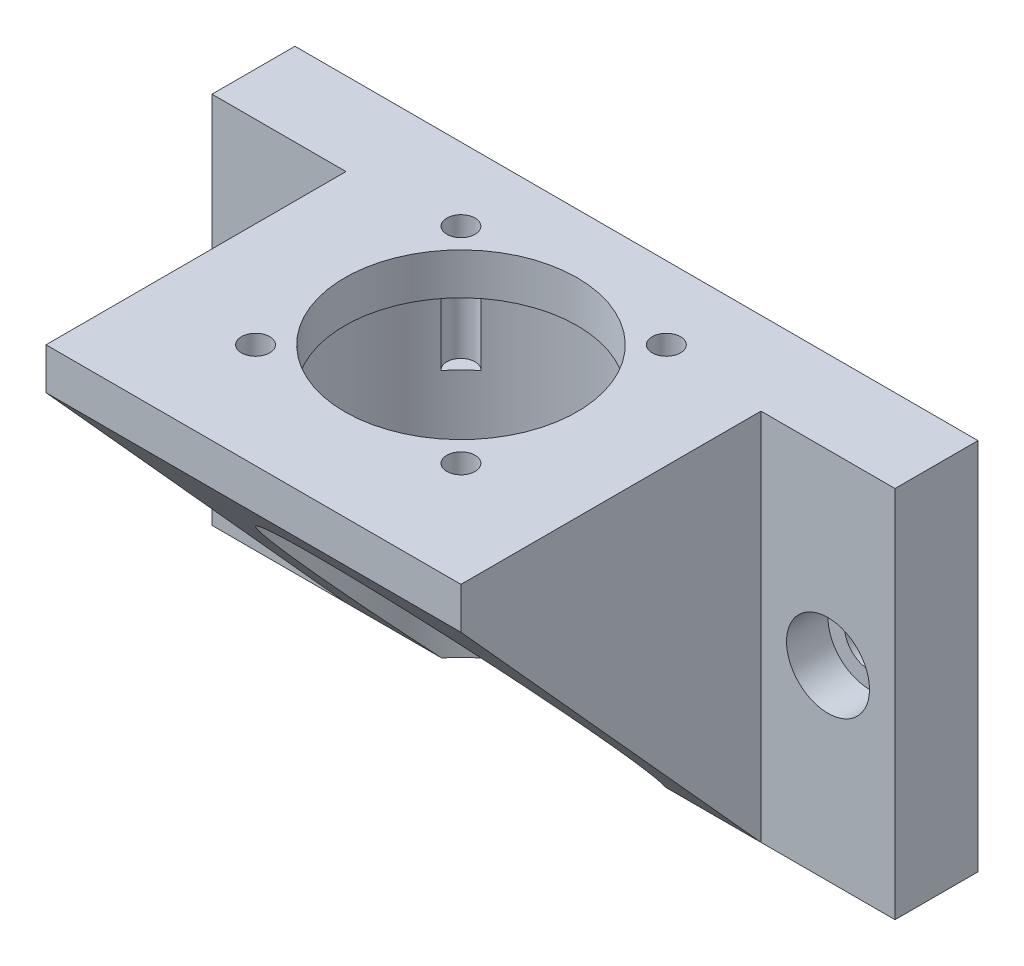
SolidWorks part; units mm, degrees
ref_plane "Спереди" through (0, 0, 0) normal (0, 0, 1) x (1, 0, 0)
ref_plane "Сверху" through (0, 0, 0) normal (0, 1, 0) x (1, 0, 0)
ref_plane "Справа" through (0, 0, 0) normal (1, 0, 0) x (0, 0, -1)
sketch "Эскиз1" plane through (0, 0, 0) normal (0, 1, 0) x (1, 0, 0)
  line L3 (-21.15, 21.15) -> (21.15, 21.15)
  line L6 (-25, 11.15) -> (-25, -25)
  line L7 (21.15, 21.15) -> (41.15, 21.15)
  line L8 (41.15, 21.15) -> (41.15, 11.15)
  line L9 (41.15, 11.15) -> (25, 11.15)
  line L10 (-21.15, 21.15) -> (-41.15, 21.15)
  line L11 (-41.15, 21.15) -> (-41.15, 11.15)
  line L12 (-41.15, 11.15) -> (-25, 11.15)
  line L13 (-25, -25) -> (25, -25)
  line L14 (25, 11.15) -> (25, -25)
  point P0 (0, 0)
  point P5 (0, 0)
  dimension "D3" = 20
  dimension "D4" = 10
  dimension "D5" = 20
  dimension "D6" = 10
extrude "Бобышка-Вытянуть1" add sketch "Эскиз1" along normal blind 45
sketch "Эскиз2" plane through (0, 0, 0) normal (0, -1, 0) x (1, 0, 0)
  circle A0 centre (0, 0) radius 17.5
  dimension "D1" = 35
extrude "Вырез-Вытянуть1" cut sketch "Эскиз2" against normal blind 40
sketch "Эскиз3" plane through (0, 40, 0) normal (0, -1, 0) x (1, 0, 0)
  circle A0 centre (0, 0) radius 14
  dimension "D1" = 28
extrude "Вырез-Вытянуть2" cut sketch "Эскиз3" against normal through all
sketch "Эскиз4" plane through (0, 40, 0) normal (0, -1, 0) x (1, 0, 0)
  line L1 (-17.5, 17.5) -> (17.5, 17.5) construction
  line L2 (-17.5, 17.5) -> (-17.5, -17.5) construction
  line L3 (-17.5, -17.5) -> (17.5, -17.5) construction
  line L4 (17.5, 17.5) -> (17.5, -17.5) construction
  line L5 (-17.5, 17.5) -> (17.5, -17.5) construction
  line L6 (-17.5, -17.5) -> (17.5, 17.5) construction
  circle A0 centre (0, 0) radius 17.5 construction
  circle A1 centre (-12.3744, -12.3744) radius 1.7
  circle A2 centre (12.3744, -12.3744) radius 1.7
  circle A3 centre (12.3744, 12.3744) radius 1.7
  circle A4 centre (-12.3744, 12.3744) radius 1.7
  point P0 (0, 0)
  dimension "D2" = 3.4
  dimension "D3" = 3.4
  dimension "D4" = 3.4
  dimension "D5" = 3.4
  dimension "D1" = 35
extrude "Вырез-Вытянуть3" cut sketch "Эскиз4" along normal blind 10 and the other way blind 14
sketch "Эскиз5" plane through (0, 0, -11.15) normal (0, 0, 1) x (1, 0, 0)
  circle A0 centre (-33.075, 22.5) radius 3
  circle A1 centre (33.075, 22.5) radius 3
  dimension "D1" = 6
  dimension "D2" = 6
extrude "Вырез-Вытянуть4" cut sketch "Эскиз5" against normal through all
sketch "Эскиз6" plane through (0, 0, -11.15) normal (0, 0, 1) x (1, 0, 0)
  circle A0 centre (-33.075, 22.5) radius 5
  circle A1 centre (33.075, 22.5) radius 5
  dimension "D1" = 10
  dimension "D2" = 10
extrude "Вырез-Вытянуть5" cut sketch "Эскиз6" against normal blind 5
sketch "Эскиз7" plane through (25, 0, 0) normal (1, 0, 0) x (0, 0, -1)
  line L0 (-29.9278, 45) -> (-29.9278, 40) construction
  line L1 (-25, 40) -> (11.15, 0)
  line L2 (-25, 45) -> (-25, 0) construction
  line L3 (11.15, 45) -> (11.15, 0) construction
  line L4 (11.15, 45) -> (11.15, 0) construction
  line L5 (11.15, 0) -> (-25, 0)
  line L6 (-25, 0) -> (-25, 40)
  dimension "D1" = 5
extrude "Вырез-Вытянуть6" cut sketch "Эскиз7" against normal through all
